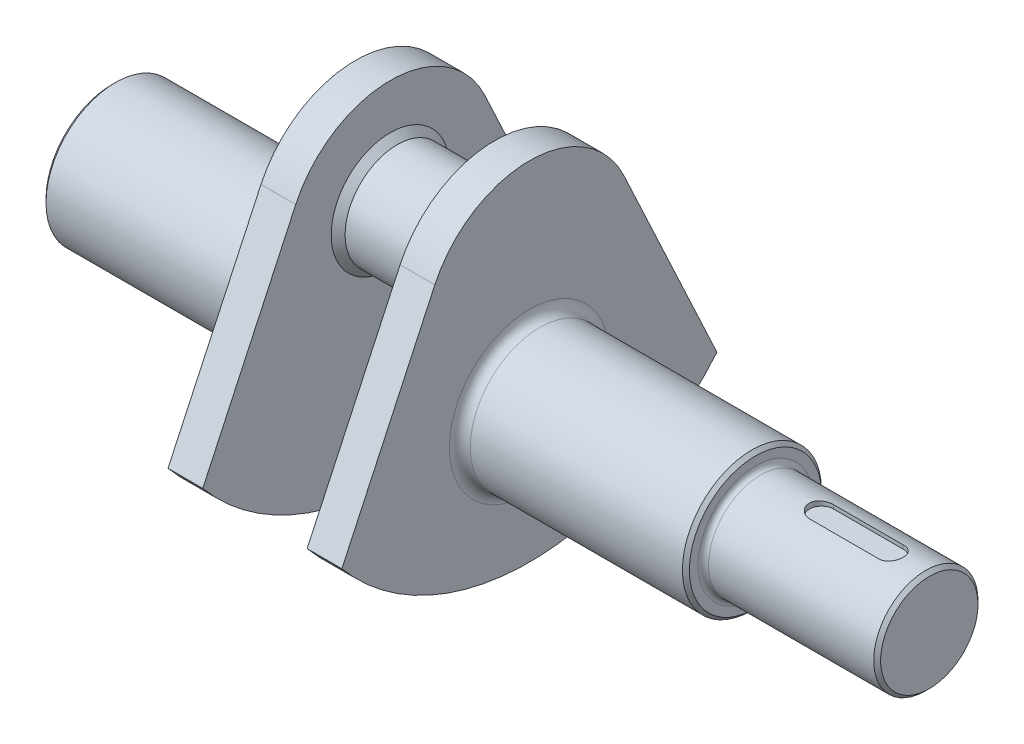
SolidWorks part; units mm, degrees
material "Dökme Alaşımlı Çelik"
ref_plane "Ön Düzlem" through (0, 0, 0) normal (0, 0, 1) x (1, 0, 0)
ref_plane "Üst Düzlem" through (0, 0, 0) normal (0, 1, 0) x (1, 0, 0)
ref_plane "Sağ Düzlem" through (0, 0, 0) normal (1, 0, 0) x (0, 0, -1)
sketch "Çizim1" plane through (0, 0, 0) normal (0, 0, 1) x (1, 0, 0)
  line L0 (0, 0) -> (-32.5879, 0) construction
  line L1 (0, 0) -> (0, 19)
  line L2 (1, 20) -> (67, 20)
  line L3 (0, 19) -> (1, 20)
  line L4 (0, 0) -> (105.4791, 0) construction
  line L5 (70, 23) -> (70, 80)
  line L6 (70, 80) -> (80, 80)
  line L7 (80, 80) -> (80, 0)
  line L8 (80, 0) -> (80, -40)
  line L9 (80, -40) -> (70, -40)
  line L10 (70, -40) -> (70, -23)
  line L11 (67, -20) -> (0, -20)
  line L12 (0, -20) -> (0, 0)
  line L13 (0, 0) -> (80, 0)
  arc A0 (67, 20) -> (70, 23) centre (67, 23) ccw
  arc A1 (70, -23) -> (67, -20) centre (67, -23) ccw
  point P4 (0, 20)
  point P13 (70, 20)
  point P20 (70, -20)
  dimension "D6" = 3
  dimension "D11" = 3
  dimension "D1" = 20
  dimension "D2" = 70
  dimension "D3" = 60
  dimension "D4" = 10
  dimension "D7" = 40
  dimension "D8" = 10
  dimension "D9" = 20
  dimension "D10" = 70
revolve "Döndür2" add sketch "Çizim1" angle 360 about L4
sketch "Çizim2" plane through (70, 0, 0) normal (-1, 0, 0) x (0, 0, 1)
  line L0 (0, 0) -> (0, 30) construction
  line L1 (-53.918, -14.6414) -> (-27.1892, 42.6785)
  line L2 (53.918, -14.6414) -> (27.1892, 42.6785)
  circle A2 centre (0, 0) radius 19 construction
  circle A3 centre (0, 0) radius 19
  circle A6 centre (0, 30) radius 15 construction
  arc A7 (-53.918, -14.6414) -> (53.918, -14.6414) centre (0, 30) ccw
  circle A8 centre (0, 30) radius 30
  circle A9 centre (0, 0) radius 80 construction
  circle A10 centre (0, 0) radius 80
  point P11 (-22.9824, 49.2824)
  point P12 (27.3212, 42.964)
  circle M1 centre (0, 0) radius 80
  dimension "D1" = 30
  dimension "D2" = 30
  dimension "D3" = 140
  dimension "D4" = 60
  dimension "D5" = 50
extrude "Kes-Ekstrüzyon1" cut sketch "Çizim2" against normal blind 10 contours A8 L2 A7 L1 M1
sketch "Çizim3" plane through (80, 0, 0) normal (1, 0, 0) x (0, 0, -1)
  circle A0 centre (0, 30) radius 15
  dimension "D1" = 30
extrude "Yükseklik-Ekstrüzyon1" add sketch "Çizim3" along normal blind 30
ref_plane "Düzlem3" through (95, 0, 0) normal (1, 0, 0) x (0, 0, -1)
mirror "Aynalama3" about plane through (95, 0, 0) normal (1, 0, 0) of "Döndür2"
sketch "Çizim4" plane through (120, 0, 0) normal (1, 0, 0) x (0, 0, -1)
  line L0 (0, 0) -> (0, 30) construction
  line L1 (-53.918, -14.6414) -> (-27.1892, 42.6785)
  line L2 (53.918, -14.6414) -> (27.1892, 42.6785)
  arc A0 (-53.918, -14.6414) -> (53.918, -14.6414) centre (0, 30) ccw
  circle A1 centre (0, 30) radius 30
  circle A2 centre (0, 0) radius 80 construction
  circle A3 centre (0, 0) radius 80
  point P9 (27.3405, 43.0063)
  circle M4 centre (0, 0) radius 80
  dimension "D2" = 140
  dimension "D3" = 60
  dimension "D1" = 30
  dimension "D4" = 50
extrude "Kes-Ekstrüzyon2" cut sketch "Çizim4" against normal blind 10 contours A1 L2 A0 L1 M4
chamfer "Pah1" distance 2 angle 45 2 edges at (110, 30, -15) (80, 30, -15)
sketch "Çizim5" plane through (190, 0, 0) normal (1, 0, 0) x (0, 0, -1)
  circle A0 centre (0, 0) radius 20 construction
  circle A1 centre (0, 0) radius 20
extrude "Kes-Ekstrüzyon3" cut sketch "Çizim5" against normal blind 5
sketch "Çizim6" plane through (185, 0, 0) normal (1, 0, 0) x (0, 0, -1)
  circle A0 centre (0, 0) radius 15
  dimension "D1" = 30
extrude "Yükseklik-Ekstrüzyon2" add sketch "Çizim6" along normal blind 50
chamfer "Pah2" distance 1 angle 45 1 edges at (235, 0, -15)
fillet "Radyus1" radius 1.5 1 edges at (185, 0, -15)
chamfer "Pah3" distance 1 angle 45 1 edges at (185, 0, -20)
ref_plane "Düzlem4" through (0, 15, 0) normal (0, 1, 0) x (1, 0, 0)
sketch "Çizim7" plane through (0, 15, 0) normal (0, 1, 0) x (1, 0, 0)
  line L0 (234, 0) -> (224, 0) construction
  line L1 (234, 15) -> (234, -15) construction
  line L2 (224, 0) -> (204, 0) construction
  line L3 (224, -3.5) -> (204, -3.5)
  line L4 (224, 3.5) -> (204, 3.5)
  arc A0 (224, -3.5) -> (224, 3.5) centre (224, 0) ccw
  arc A1 (204, 3.5) -> (204, -3.5) centre (204, 0) ccw
  point P5 (214, 0)
  dimension "D3" = 3.5
  dimension "D1" = 10
  dimension "D2" = 20
extrude "Kes-Ekstrüzyon4" cut sketch "Çizim7" against normal blind 1.5
